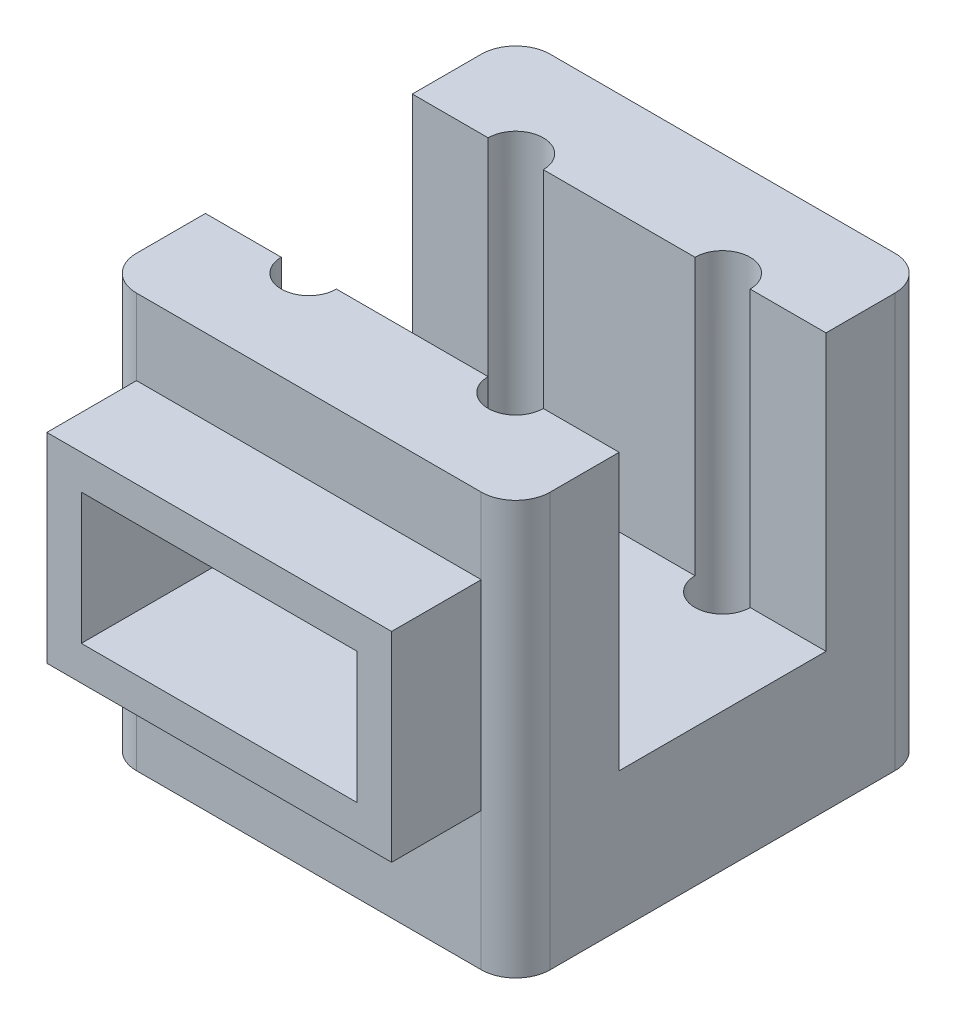
SolidWorks part; units mm, degrees
ref_plane "Front Plane" through (0, 0, 0) normal (0, 0, 1) x (1, 0, 0)
ref_plane "Top Plane" through (0, 0, 0) normal (0, 1, 0) x (1, 0, 0)
ref_plane "Right Plane" through (0, 0, 0) normal (1, 0, 0) x (0, 0, -1)
sketch "Sketch1" plane through (0, 0, 0) normal (0, 1, 0) x (1, 0, 0)
  line L1 (-30, 30) -> (30, 30)
  line L2 (-30, 30) -> (-30, -30)
  line L3 (-30, -30) -> (30, -30)
  line L4 (30, 30) -> (30, -30)
  line L5 (-30, 30) -> (30, -30) construction
  line L6 (-30, -30) -> (30, 30) construction
  circle A0 centre (-15, 15) radius 2
  circle A1 centre (15, 15) radius 2
  circle A2 centre (15, -15) radius 2
  circle A3 centre (-15, -15) radius 2
  point P0 (0, 0)
  dimension "D9" = 4
  dimension "D10" = 4
  dimension "D11" = 4
  dimension "D12" = 4
  dimension "D1" = 60
  dimension "D2" = 60
  dimension "D3" = 30
  dimension "D4" = 30
  dimension "D5" = 15
  dimension "D6" = 15
  dimension "D7" = 30
  dimension "D8" = 15
extrude "Boss-Extrude1" add sketch "Sketch1" along normal blind 60
sketch "Sketch2" plane through (0, 60, 0) normal (0, 1, 0) x (1, 0, 0)
  circle A0 centre (-15, 15) radius 4
  circle A1 centre (15, 15) radius 4
  circle A2 centre (15, -15) radius 4
  circle A3 centre (-15, -15) radius 4
  dimension "D1" = 8
  dimension "D2" = 8
  dimension "D3" = 8
  dimension "D4" = 8
extrude "Cut-Extrude1" cut sketch "Sketch2" against normal blind 50
fillet "Fillet1" radius 5 4 edges at (-30, 30, -30) (-30, 30, 30) (30, 30, -30) (30, 30, 30)
sketch "Sketch3" plane through (30, 0, 0) normal (1, 0, 0) x (0, 0, -1)
  line L0 (-25, 60) -> (25, 60) construction
  line L1 (-15, 60) -> (15, 60)
  line L2 (-15, 60) -> (-15, 20)
  line L3 (-15, 20) -> (15, 20)
  line L4 (15, 60) -> (15, 20)
  line L5 (-30, 0) -> (-30, 60) construction
  line L6 (30, 60) -> (30, 0) construction
  line L7 (-25, 0) -> (25, 0) construction
  dimension "D1" = 15
  dimension "D2" = 15
  dimension "D3" = 30
  dimension "D4" = 20
extrude "Cut-Extrude2" cut sketch "Sketch3" against normal through all
sketch "Sketch4" plane through (0, 0, 30) normal (0, 0, 1) x (1, 0, 0)
  line L0 (-30, 0) -> (-30, 60) construction
  line L1 (-20, 44) -> (20, 44)
  line L2 (-20, 44) -> (-20, 25)
  line L3 (-20, 25) -> (20, 25)
  line L4 (20, 44) -> (20, 25)
  line L5 (-25, 0) -> (25, 0) construction
  dimension "D1" = 40
  dimension "D2" = 19
  dimension "D3" = 10
  dimension "D4" = 25
extrude "Cut-Extrude3" cut sketch "Sketch4" against normal blind 30
sketch "Sketch5" plane through (0, 0, 30) normal (0, 0, 1) x (1, 0, 0)
  line L0 (-25, 60) -> (-25, 0) construction
  line L1 (-25, 49) -> (25, 49)
  line L2 (-25, 49) -> (-25, 20)
  line L3 (-25, 20) -> (25, 20)
  line L4 (25, 49) -> (25, 20)
  line L5 (25, 0) -> (25, 60) construction
  line L6 (20, 44) -> (-20, 44) construction
  line L7 (-20, 25) -> (20, 25) construction
  line L9 (-20, 44) -> (20, 44)
  line L10 (-20, 44) -> (-20, 25)
  line L11 (-20, 25) -> (20, 25)
  line L12 (20, 44) -> (20, 25)
  dimension "D1" = 5
  dimension "D2" = 5
extrude "Boss-Extrude3" add sketch "Sketch5" along normal blind 13
sketch "Sketch6" plane through (0, 0, -30) normal (0, 0, -1) x (-1, 0, 0)
  line L0 (-25, 60) -> (25, 60) construction
  circle A0 centre (0, 40) radius 10
  dimension "D1" = 20
  dimension "D2" = 20
extrude "Cut-Extrude4" cut sketch "Sketch6" against normal blind 10
